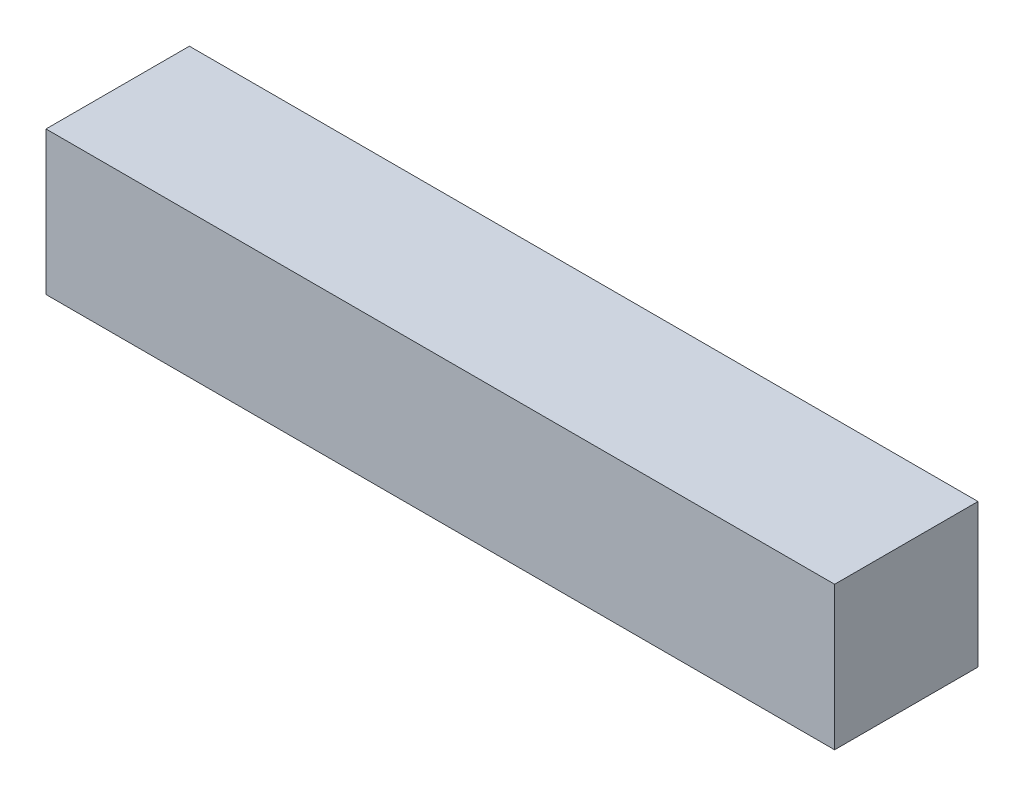
SolidWorks part; units mm, degrees
ref_plane "Front Plane" through (0, 0, 0) normal (0, 0, 1) x (1, 0, 0)
ref_plane "Top Plane" through (0, 0, 0) normal (0, 1, 0) x (1, 0, 0)
ref_plane "Right Plane" through (0, 0, 0) normal (1, 0, 0) x (0, 0, -1)
sketch "Sketch1" plane through (0, 0, 0) normal (0, 0, 1) x (1, 0, 0)
  line L1 (0, 0) -> (17.4625, 0)
  line L2 (0, 0) -> (0, 3.175)
  line L3 (0, 3.175) -> (17.4625, 3.175)
  line L4 (17.4625, 0) -> (17.4625, 3.175)
  dimension "D1" = 3.175
  dimension "D2" = 17.4625
extrude "Boss-Extrude1" add sketch "Sketch1" along normal blind 3.175
